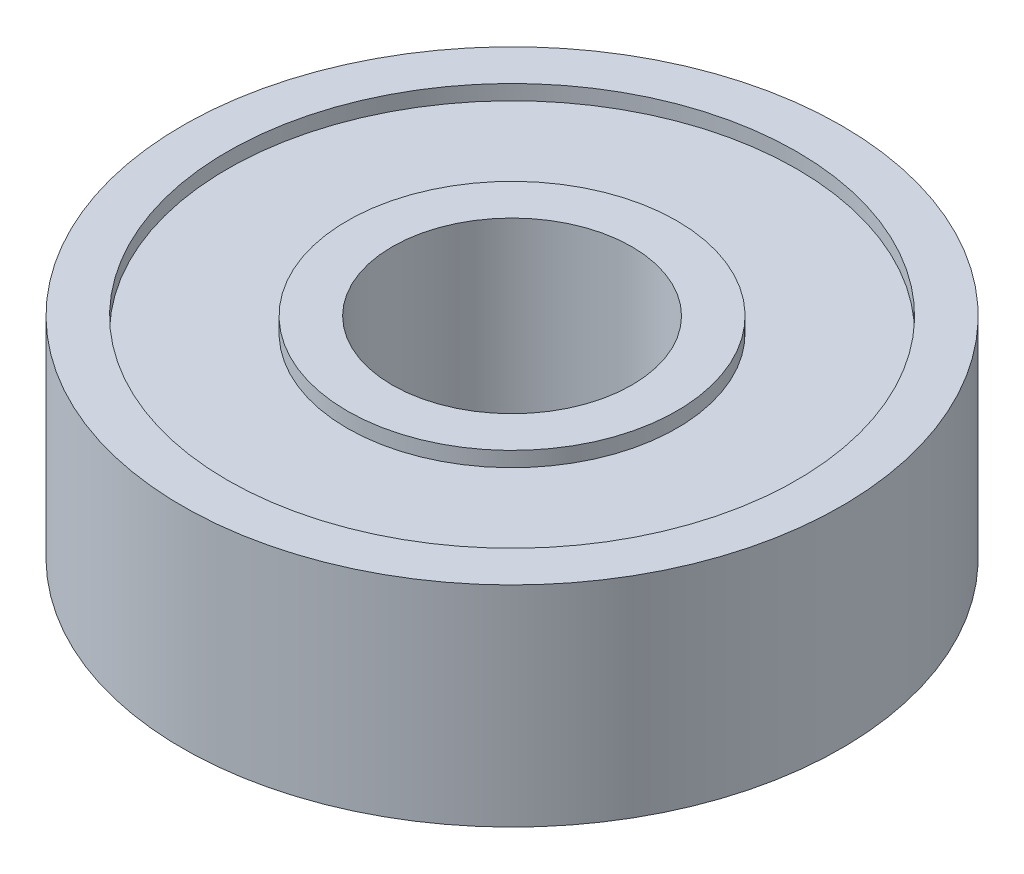
SolidWorks part; units mm, degrees
ref_plane "Front Plane" through (0, 0, 0) normal (0, 0, 1) x (1, 0, 0)
ref_plane "Top Plane" through (0, 0, 0) normal (0, 1, 0) x (1, 0, 0)
ref_plane "Right Plane" through (0, 0, 0) normal (1, 0, 0) x (0, 0, -1)
sketch "Sketch1" plane through (0, 0, 0) normal (0, 0, 1) x (1, 0, 0)
  line L0 (0, -3.3627) -> (0, 8.371) construction
  line L1 (0, 0) -> (-2.2752, 0) construction
  line L2 (-5.5, 3.5) -> (-4, 3.5)
  line L3 (-5.5, 3.5) -> (-5.5, -3.5)
  line L4 (-5.5, -3.5) -> (-4, -3.5)
  line L5 (-4, 3.5) -> (-4, -3.5)
  line L6 (-11, 3.5) -> (-9.5, 3.5)
  line L7 (-11, 3.5) -> (-11, -3.5)
  line L8 (-11, -3.5) -> (-9.5, -3.5)
  line L9 (-9.5, 3.5) -> (-9.5, -3.5)
  line L10 (-9.5, -3) -> (-5.5, -3)
  line L11 (-9.5, -3) -> (-9.5, 3)
  line L12 (-9.5, 3) -> (-5.5, 3)
  line L13 (-5.5, -3) -> (-5.5, 3)
  point P11 (-4, 0)
  point P12 (-9.5, 0)
  dimension "D1" = 8
  dimension "D2" = 7
  dimension "D3" = 22
  dimension "D4" = 1.5
  dimension "D5" = 0.5
revolve "Revolve1" add sketch "Sketch1" angle 360 about L0
